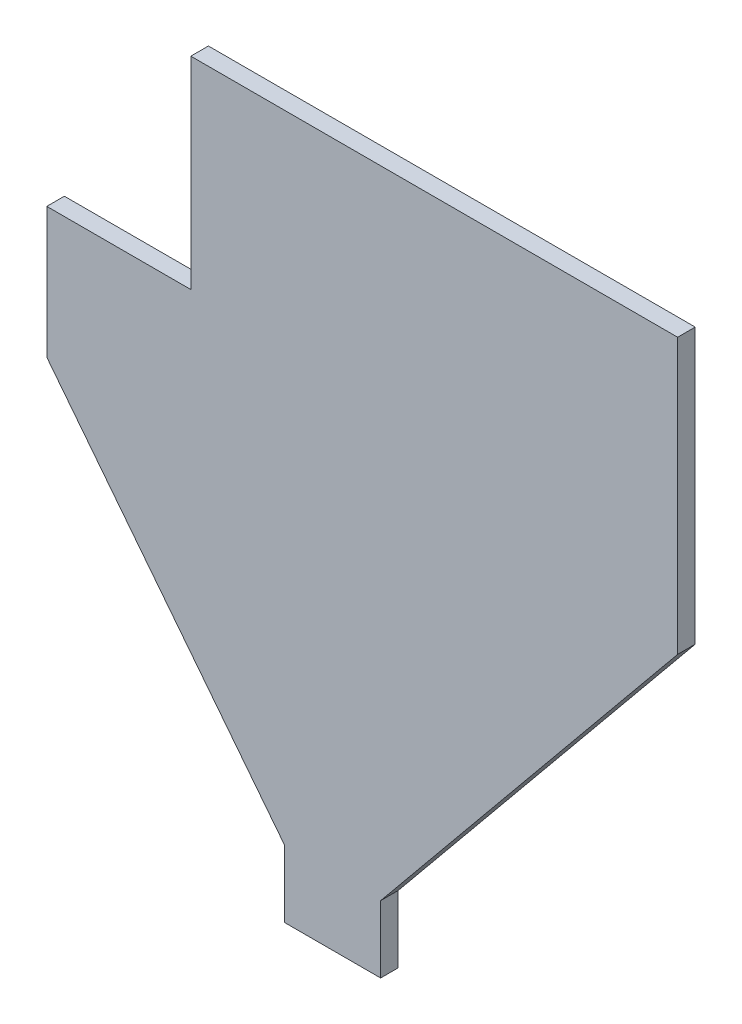
SolidWorks part; units mm, degrees
ref_plane "Plan de face" through (0, 0, 0) normal (0, 0, 1) x (1, 0, 0)
ref_plane "Plan de dessus" through (0, 0, 0) normal (0, 1, 0) x (1, 0, 0)
ref_plane "Plan de droite" through (0, 0, 0) normal (1, 0, 0) x (0, 0, -1)
sketch "Esquisse1" plane through (0, 0, 0) normal (0, 0, 1) x (1, 0, 0)
  line L0 (-16.129, -1.27) -> (-16.129, -24.257)
  line L1 (-16.129, -24.257) -> (-32.512, -24.257)
  line L2 (-32.512, -24.257) -> (-32.512, -39.116)
  line L3 (-32.512, -39.116) -> (-5.461, -73.66)
  line L4 (-5.461, -73.66) -> (-5.461, -81.28)
  line L5 (-5.461, -81.28) -> (5.461, -81.28)
  line L6 (5.461, -81.28) -> (5.461, -73.66)
  line L7 (5.461, -73.66) -> (39.243, -32.512)
  line L8 (39.243, -32.512) -> (39.243, -1.27)
  line L9 (39.243, -1.27) -> (-16.129, -1.27)
  line L10 (0, -81.28) -> (0, -1.27) construction
  point P13 (-16.129, -45.352)
  point P14 (0, 0)
  point P15 (0, -9.4316)
  point P16 (0, -10.3411)
  dimension "D1" = 16.129
  dimension "D2" = 1.27
  dimension "D3" = 39.243
  dimension "D4" = 32.512
  dimension "D5" = 5.461
  dimension "D6" = 73.66
  dimension "D7" = 81.28
  dimension "D8" = 5.461
  dimension "D9" = 39.116
  dimension "D10" = 32.512
  dimension "24.257" = 24.257
extrude "Boss.-Extru.1" add sketch "Esquisse1" along normal blind 2
